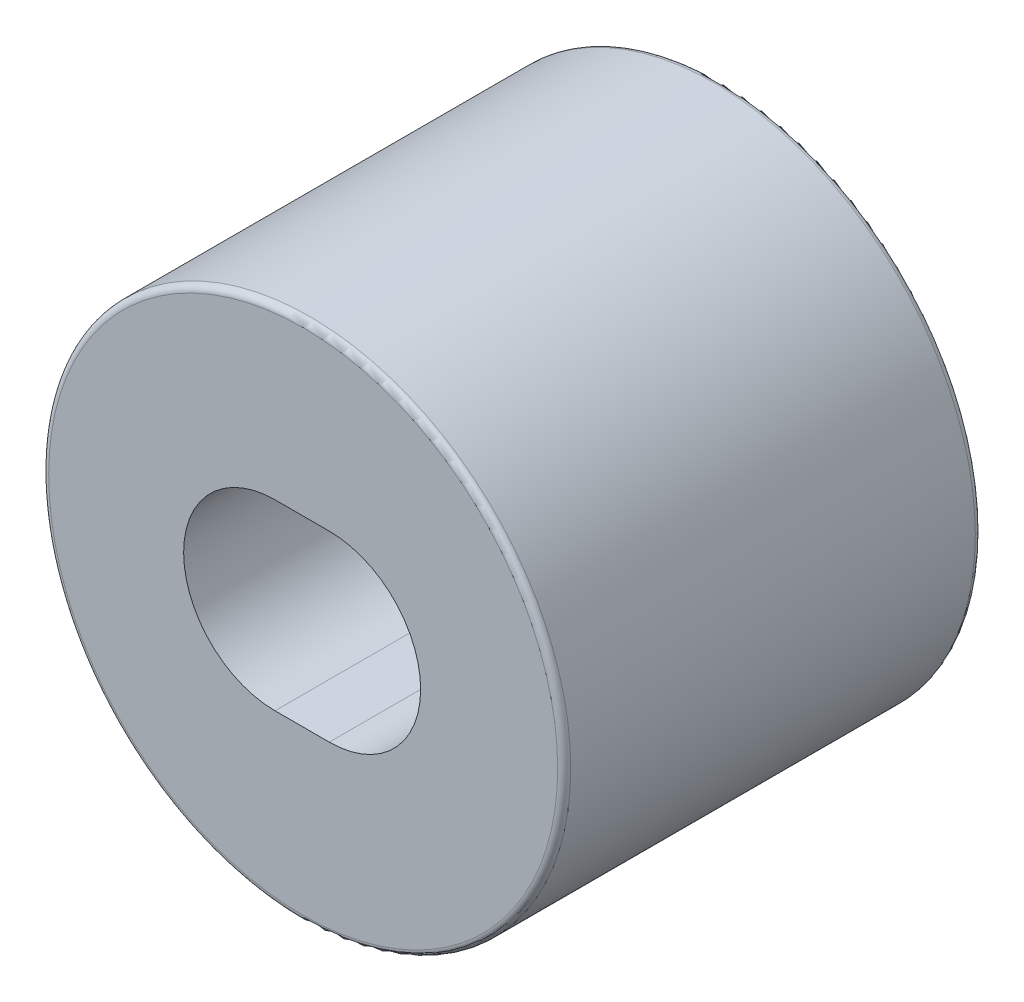
SolidWorks part; units mm, degrees
material "Brass"
ref_plane "Front Plane" through (0, 0, 0) normal (0, 0, 1) x (1, 0, 0)
ref_plane "Top Plane" through (0, 0, 0) normal (0, 1, 0) x (1, 0, 0)
ref_plane "Right Plane" through (0, 0, 0) normal (1, 0, 0) x (0, 0, -1)
sketch "Sketch1" plane through (0, 0, 0) normal (0, 0, 1) x (1, 0, 0)
  line L0 (0, 0) -> (0.5, 0)
  line L1 (0, 0) -> (-0.5, 0)
  line L2 (-0.5402, 0) -> (0.5, 0) construction
  line L3 (-0.5402, 1.75) -> (0.5, 1.75)
  line L4 (-0.5402, -1.75) -> (0.5, -1.75)
  circle A0 centre (0, 0) radius 5
  arc A3 (-0.5402, 1.75) -> (-0.5402, -1.75) centre (-0.5402, 0) ccw
  arc A4 (0.5, -1.75) -> (0.5, 1.75) centre (0.5, 0) ccw
  point P8 (-0.0201, 0)
  dimension "D1" = 10
  dimension "D2" = 0.5
  dimension "D3" = 0.5
extrude "Boss-Extrude1" add sketch "Sketch1" along normal blind 8 contours A0 A4 L4 A3 L3
fillet "Fillet1" radius 0.125 2 edges at (5, 0, 0) (5, 0, 8)
sketch "Sketch3" plane through (0, 0, 0) normal (0, 0, 1) x (1, 0, 0)
  line L0 (0, -5) -> (3.3506, -5)
  circle A0 centre (0, 0) radius 5 construction
ref_plane "Plane1" through (0, -5, 0) normal (0, -1, 0) x (1, 0, 0)
sketch "Sketch4" plane through (0, -5, 0) normal (0, -1, 0) x (1, 0, 0)
  line L0 (4.875, 8) -> (-4.875, 8) construction
  circle A0 centre (0, 4) radius 2
  dimension "D2" = 4
  dimension "D1" = 4
extrude "Cut-Extrude1" cut sketch "Sketch4" against normal blind 2.5
